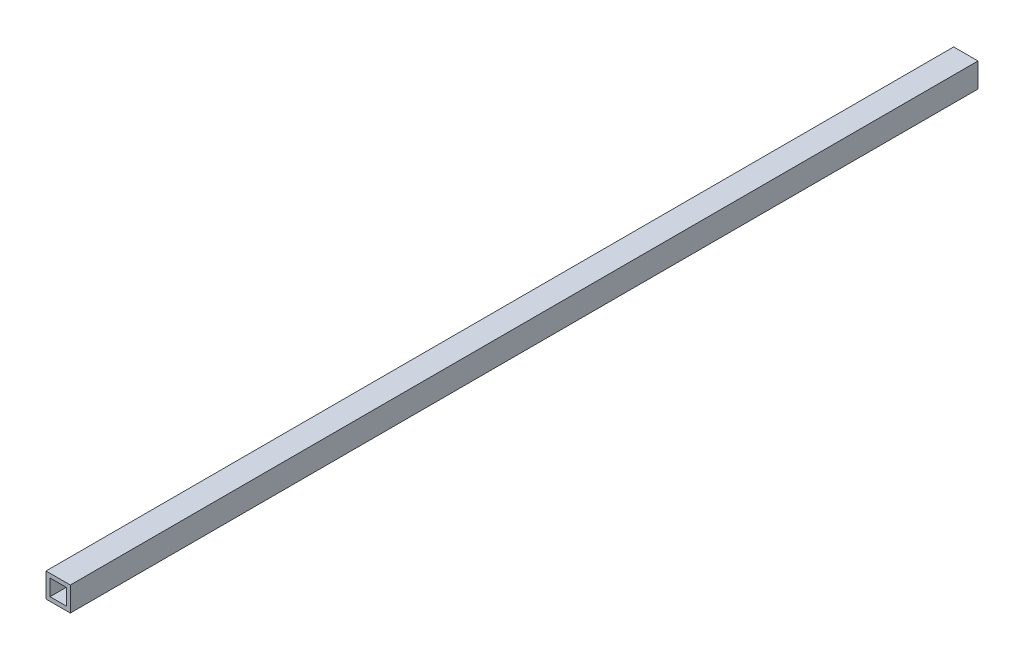
SolidWorks part; units mm, degrees
ref_plane "Front Plane" through (0, 0, 0) normal (0, 0, 1) x (1, 0, 0)
ref_plane "Top Plane" through (0, 0, 0) normal (0, 1, 0) x (1, 0, 0)
ref_plane "Right Plane" through (0, 0, 0) normal (1, 0, 0) x (0, 0, -1)
sketch "Sketch1" plane through (0, 0, 0) normal (0, 0, 1) x (1, 0, 0)
  line L1 (-9.525, -9.525) -> (9.525, -9.525)
  line L2 (-9.525, -9.525) -> (-9.525, 9.525)
  line L3 (-9.525, 9.525) -> (9.525, 9.525)
  line L4 (9.525, -9.525) -> (9.525, 9.525)
  line L5 (-9.525, -9.525) -> (9.525, 9.525) construction
  line L6 (-9.525, 9.525) -> (9.525, -9.525) construction
  point P0 (0, 0)
  dimension "D1" = 19.05
  dimension "D2" = 19.05
extrude "Boss-Extrude1" add sketch "Sketch1" against normal blind 711.2
sketch "Sketch2" plane through (0, 0, 0) normal (0, 0, 1) x (1, 0, 0)
  line L1 (-6.35, -6.35) -> (6.35, -6.35)
  line L2 (-6.35, -6.35) -> (-6.35, 6.35)
  line L3 (-6.35, 6.35) -> (6.35, 6.35)
  line L4 (6.35, -6.35) -> (6.35, 6.35)
  line L5 (-6.35, -6.35) -> (6.35, 6.35) construction
  line L6 (-6.35, 6.35) -> (6.35, -6.35) construction
  point P0 (0, 0)
  dimension "D1" = 12.7
  dimension "D2" = 12.7
extrude "Cut-Extrude1" cut sketch "Sketch2" against normal up to next
equation "\"D2@Sketch1\"=\"D1@Sketch1\""
equation "\"D2@Sketch2\"=\"D1@Sketch2\""
